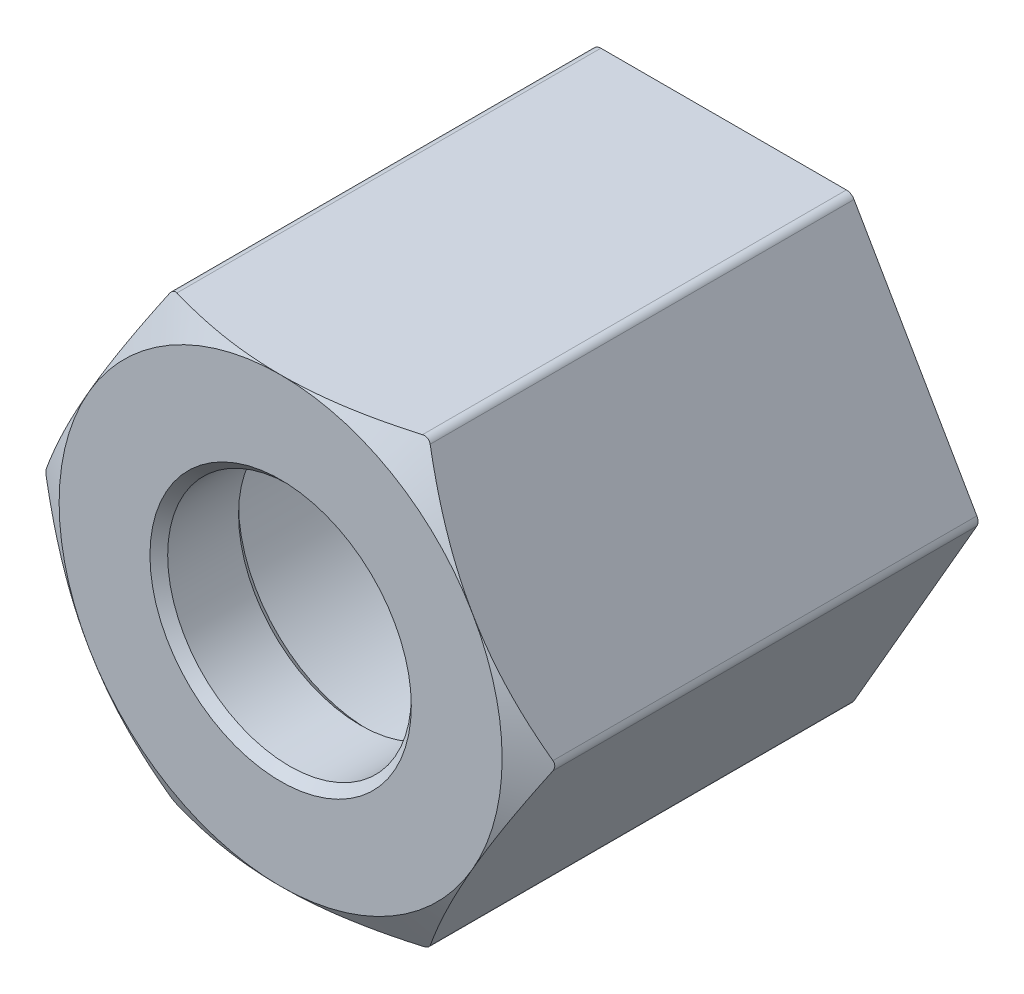
SolidWorks part; units mm, degrees
material "Acciaio inossidabile (ferroso)"
ref_plane "Piano frontale" through (0, 0, 0) normal (0, 0, 1) x (1, 0, 0)
ref_plane "Piano superiore" through (0, 0, 0) normal (0, 1, 0) x (1, 0, 0)
ref_plane "Piano destro" through (0, 0, 0) normal (1, 0, 0) x (0, 0, -1)
sketch "Schizzo4" plane through (0, 0, 0) normal (0, 0, 1) x (1, 0, 0)
  line L1 (2.8868, 5) -> (-2.8868, 5)
  line L2 (-2.8868, 5) -> (-5.7735, 0)
  line L3 (-5.7735, 0) -> (-2.8868, -5)
  line L4 (-2.8868, -5) -> (2.8868, -5)
  line L5 (2.8868, -5) -> (5.7735, 0)
  line L6 (5.7735, 0) -> (2.8868, 5)
  circle A0 centre (0, 0) radius 5 construction
  dimension "D1" = 10
extrude "Estrusione-Estrusione1" add sketch "Schizzo4" against normal blind 10 contours L2 L3 L4 L5 L6 L1
sketch "Schizzo6" plane through (0, 0, 0) normal (0, 0, 1) x (1, 0, 0)
  circle A0 centre (0, 0) radius 5
  dimension "D1" = 10
extrude "Taglio-Estrusione1" cut sketch "Schizzo6" against normal blind 0.5 draft 59 flip side to cut
fillet "Raccordo1" radius 0.2 6 edges at (2.8868, -5, -5.2324) (-2.8868, -5, -5.2324) (-5.7735, 0, -5.2324) (-2.8868, 5, -5.2324) (2.8868, 5, -5.2324) (5.7735, 0, -5.2324)
sketch "Schizzo19" plane through (0, 0, -10) normal (0, 0, -1) x (-1, 0, 0)
  circle A0 centre (0, 0) radius 4
  dimension "D1" = 8
extrude "Taglio-Estrusione5" cut sketch "Schizzo19" against normal blind 8 contours A0
cosmetic thread "Filettatura cosmetica2" parameters "D2"=10
sketch "Schizzo20" plane through (0, 0, -2) normal (0, 0, -1) x (-1, 0, 0)
  circle A0 centre (0, 0) radius 2.75
  dimension "D1" = 5.5
extrude "Taglio-Estrusione6" cut sketch "Schizzo20" against normal up to next contours A0
chamfer "Smusso3" distance 0.2 angle 45 3 edges at (-4, 0, -10) (-2.75, 0, -2) (2.75, 0, 0)
